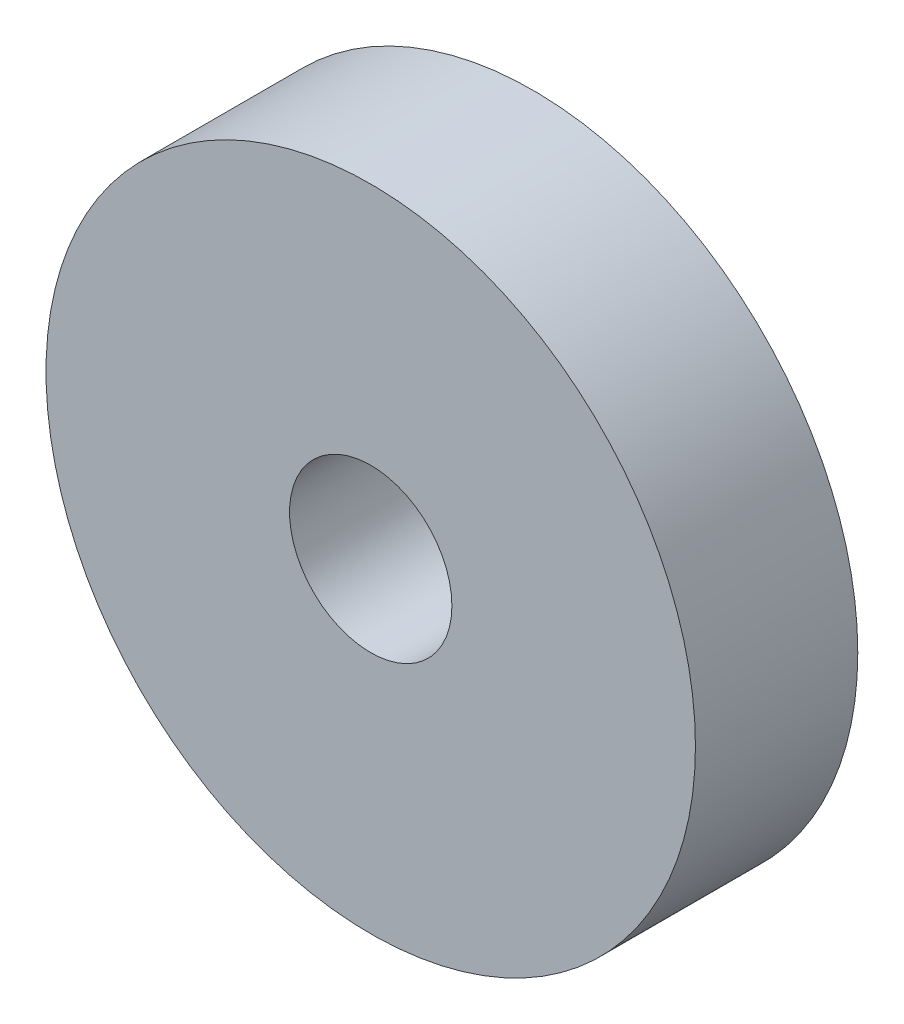
SolidWorks part; units mm, degrees
ref_plane "Front Plane" through (0, 0, 0) normal (0, 0, 1) x (1, 0, 0)
ref_plane "Top Plane" through (0, 0, 0) normal (0, 1, 0) x (1, 0, 0)
ref_plane "Right Plane" through (0, 0, 0) normal (1, 0, 0) x (0, 0, -1)
sketch "Sketch1" plane through (0, 0, 0) normal (0, 0, 1) x (1, 0, 0)
  circle A0 centre (0, 0) radius 6
  circle A1 centre (0, 0) radius 1.5
  dimension "D1" = 12
  dimension "D2" = 3
extrude "Boss-Extrude1" add sketch "Sketch1" along normal blind 3
